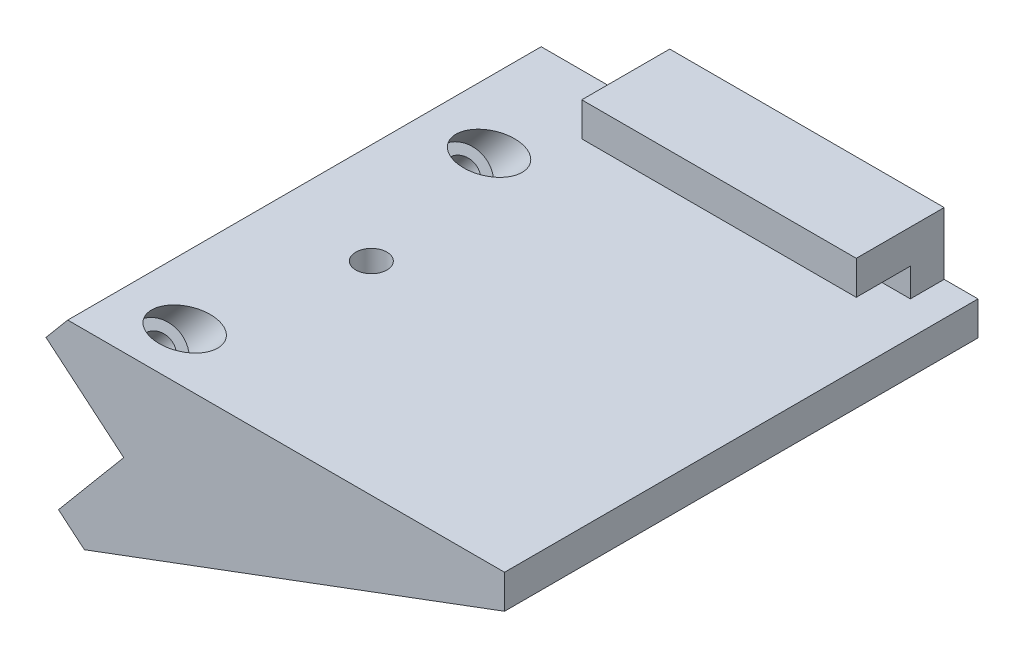
SolidWorks part; units mm, degrees
material "ABS"
ref_plane "正面" through (0, 0, 0) normal (0, 0, 1) x (1, 0, 0)
ref_plane "平面" through (0, 0, 0) normal (0, 1, 0) x (1, 0, 0)
ref_plane "右側面" through (0, 0, 0) normal (1, 0, 0) x (0, 0, -1)
sketch "ｽｹｯﾁ1" plane through (0, 0, 0) normal (0, 0, 1) x (1, 0, 0)
  line L6 (0, 0) -> (9.6418, 11.4907)
  line L7 (9.6418, 11.4907) -> (-1.8489, 21.1325)
  line L8 (-1.8489, 21.1325) -> (1.3651, 24.9627)
  line L9 (1.3651, 24.9627) -> (65.9462, 24.9627)
  line L10 (65.9462, 24.9627) -> (65.9462, 19.9627)
  line L11 (65.9462, 19.9627) -> (3.8302, -3.2139)
  line L12 (3.8302, -3.2139) -> (0, 0)
  line L13 (9.6418, 11.4907) -> (20.9462, 24.9627) construction
  dimension "D1" = 15
  dimension "D2" = 15
  dimension "D3" = 50
  dimension "D4" = 5
  dimension "D5" = 5
  dimension "D6" = 5
  dimension "0" = 45
extrude "ﾎﾞｽ - 押し出し1" add sketch "ｽｹｯﾁ1" along normal blind 65
sketch "ｽｹｯﾁ4" plane through (9.6418, 11.4907, 0) normal (-0.6428, -0.766, 0) x (-0.766, 0.6428, 0)
  line L0 (15, -65) -> (15, 0) construction
  line L1 (15, 0) -> (0, 0) construction
  line L2 (15, -65) -> (0, -65) construction
  circle A0 centre (7.5, -12.5) radius 2.25
  circle A1 centre (7.5, -57.5) radius 2.25
  dimension "D1" = 7.5
  dimension "D2" = 12.5
  dimension "D3" = 4.5
  dimension "D4" = 7.5
  dimension "D6" = 4.5
  dimension "D5" = 7.5
extrude "ｶｯﾄ - 押し出し2" cut sketch "ｽｹｯﾁ4" against normal blind 44
sketch "ｽｹｯﾁ5" plane through (9.6418, 11.4907, 0) normal (-0.6428, -0.766, 0) x (-0.766, 0.6428, 0)
  circle A0 centre (7.5, -57.5) radius 3.75
  circle A1 centre (7.5, -12.5) radius 3.75
  dimension "D1" = 7.5
  dimension "D2" = 7.5
extrude "ｶｯﾄ - 押し出し3" cut sketch "ｽｹｯﾁ5" against normal blind 44 from offset 5 offset against normal yes
sketch "ｽｹｯﾁ6" plane through (0, 0, 0) normal (0, 0, 1) x (1, 0, 0)
  line L0 (0, 0) -> (3.8302, -3.2139)
  line L1 (0, 0) -> (3.8302, -3.2139) construction
  line L2 (3.8302, -3.2139) -> (65.9462, 19.9627)
  line L3 (65.9462, 19.9627) -> (65.9462, 34.1627)
  line L4 (65.9462, 34.1627) -> (9.0848, 34.1627)
  line L5 (9.0848, 34.1627) -> (-1.8489, 21.1325)
  line L6 (-1.8489, 21.1325) -> (9.6418, 11.4907)
  line L7 (9.6418, 11.4907) -> (0, 0)
  line L10 (1.3651, 24.9627) -> (-1.8489, 21.1325) construction
  line L11 (65.9462, 24.9627) -> (1.3651, 24.9627) construction
  dimension "D1" = 9.2
extrude "ﾎﾞｽ - 押し出し2" add sketch "ｽｹｯﾁ6" against normal blind 5
sketch "ｽｹｯﾁ8" plane through (0, 0, 0) normal (0, 0, 1) x (1, 0, 0)
  line L0 (65.9462, 34.1627) -> (65.9462, 29.1627)
  line L1 (65.9462, 24.9627) -> (65.9462, 34.1627) construction
  line L2 (65.9462, 29.1627) -> (4.8893, 29.1627)
  line L3 (9.0848, 34.1627) -> (1.3651, 24.9627) construction
  line L4 (4.8893, 29.1627) -> (9.0848, 34.1627)
  line L5 (9.0848, 34.1627) -> (65.9462, 34.1627)
  dimension "D1" = 5
extrude "ﾎﾞｽ - 押し出し4" add sketch "ｽｹｯﾁ8" along normal blind 8
sketch "ｽｹｯﾁ9" plane through (0, 24.9627, 0) normal (0, 1, 0) x (1, 0, 0)
  line L0 (1.3651, 0) -> (1.3651, -65) construction
  line L2 (65.9462, -65) -> (1.3651, -65) construction
  circle A0 centre (16.2551, -35) radius 2.3
  dimension "D1" = 4.6
  dimension "D3" = 30
  dimension "D2" = 14.89
extrude "ｶｯﾄ - 押し出し4" cut sketch "ｽｹｯﾁ9" against normal blind 3.5
sketch "ｽｹｯﾁ11" plane through (0, 0, 8) normal (0, 0, 1) x (1, 0, 0)
  line L0 (1.3651, 24.9627) -> (20.3648, 24.9627)
  line L1 (65.9462, 24.9627) -> (1.3651, 24.9627) construction
  line L2 (20.3648, 24.9627) -> (20.3648, 34.1627)
  line L3 (65.9462, 34.1627) -> (9.0848, 34.1627) construction
  line L4 (20.3648, 34.1627) -> (9.0848, 34.1627)
  line L5 (9.0848, 34.1627) -> (1.3651, 24.9627)
  dimension "D1" = 11.28
extrude "ｶｯﾄ - 押し出し6" cut sketch "ｽｹｯﾁ11" against normal through all
sketch "ｽｹｯﾁ12" plane through (65.9462, 0, 0) normal (1, 0, 0) x (0, 0, -1)
  line L0 (0, 24.9627) -> (5, 24.9627)
  line L1 (5, 24.9627) -> (5, 34.1627)
  line L2 (0, 24.9627) -> (0, 29.1627) construction
  line L3 (-8, 29.1627) -> (0, 29.1627) construction
  line L4 (-8, 29.1627) -> (-8, 34.1627) construction
  line L5 (5, 34.1627) -> (-8, 34.1627) construction
  line L6 (0, 24.9627) -> (0, 29.1627)
  line L7 (-8, 29.1627) -> (0, 29.1627)
  line L8 (-8, 29.1627) -> (-8, 34.1627)
  line L9 (5, 34.1627) -> (-8, 34.1627)
extrude "ｶｯﾄ - 押し出し7" cut sketch "ｽｹｯﾁ12" against normal blind 5
